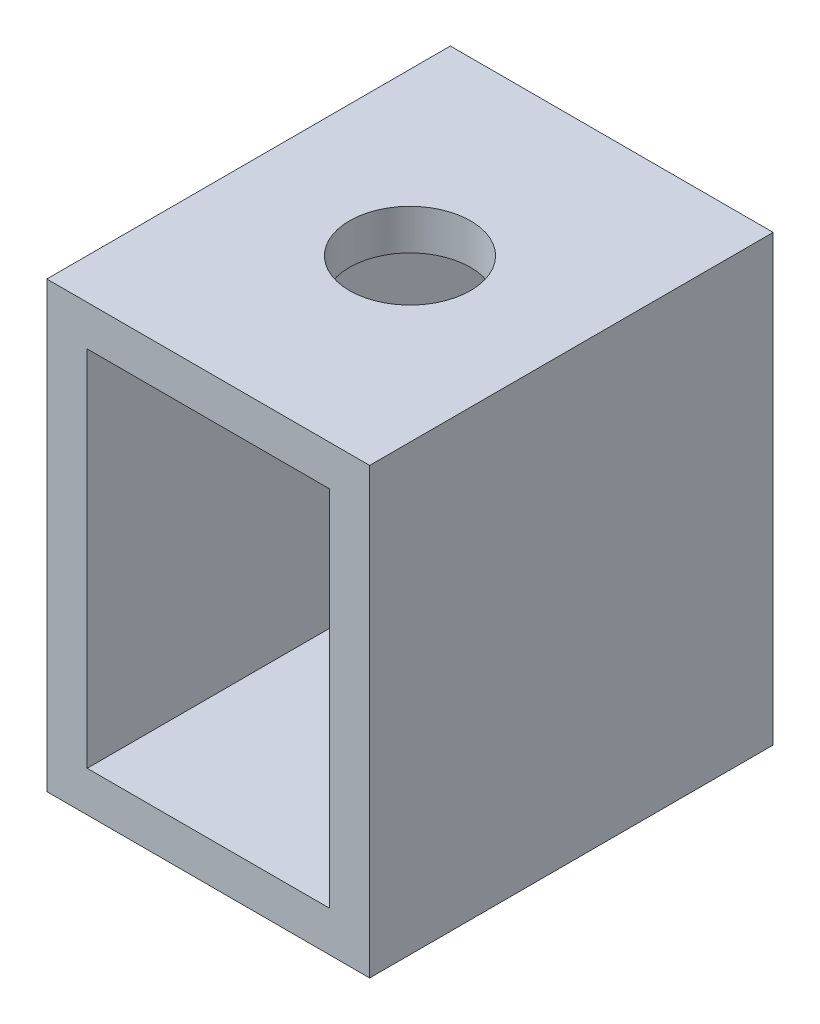
SolidWorks part; units mm, degrees
ref_plane "Front Plane" through (0, 0, 0) normal (0, 0, 1) x (1, 0, 0)
ref_plane "Top Plane" through (0, 0, 0) normal (0, 1, 0) x (1, 0, 0)
ref_plane "Right Plane" through (0, 0, 0) normal (1, 0, 0) x (0, 0, -1)
sketch "Sketch1" plane through (0, 0, 0) normal (0, 0, 1) x (1, 0, 0)
  line L1 (0, 0) -> (3, 0)
  line L2 (0, 0) -> (0, 4.5)
  line L3 (0, 4.5) -> (3, 4.5)
  line L4 (3, 0) -> (3, 4.5)
  dimension "D1" = 4.5
  dimension "D2" = 3
extrude "Extrude-Thin1" add sketch "Sketch1" along normal blind 5 thin
sketch "Sketch2" plane through (0, 5, 0) normal (0, 1, 0) x (1, 0, 0)
  line L0 (3.5, -5) -> (3.5, 0) construction
  line L1 (3.5, 0) -> (-0.5, 0) construction
  circle A0 centre (1.5, -2.5) radius 0.75
  point P5 (3.5, -2.5)
  point P9 (1.5, 0)
  dimension "D1" = 1.5
extrude "Cut-Extrude1" cut sketch "Sketch2" against normal up to next
